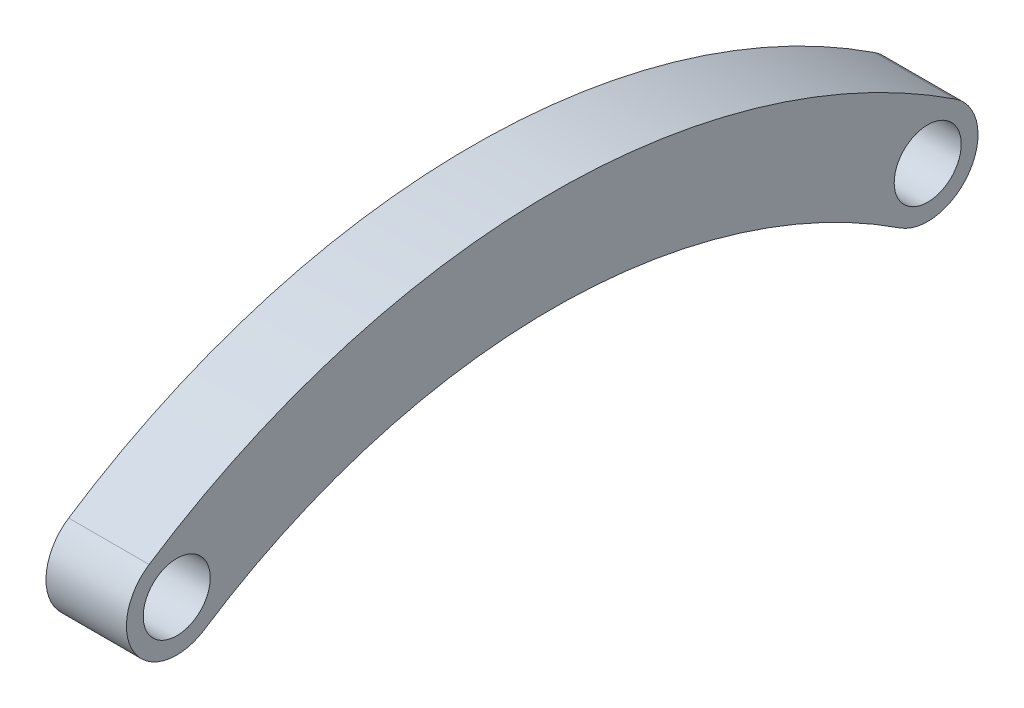
SolidWorks part; units mm, degrees
ref_plane "Front Plane" through (0, 0, 0) normal (0, 0, 1) x (1, 0, 0)
ref_plane "Top Plane" through (0, 0, 0) normal (0, 1, 0) x (1, 0, 0)
ref_plane "Right Plane" through (0, 0, 0) normal (1, 0, 0) x (0, 0, -1)
sketch "Sketch1" plane through (0, 0, 0) normal (1, 0, 0) x (0, 0, -1)
  line L0 (0, 55) -> (0, -55) construction
  line L1 (0, 0) -> (0, 6) construction
  line L2 (-22.4, -6.7) -> (22.4, -6.7) construction
  line L3 (81.1274, 6) -> (-72.2732, 6) construction
  line L4 (-25.4, 29.1562) -> (-25.4, -3.7) construction
  line L5 (25.4, 30.6853) -> (25.4, -3.7) construction
  arc A0 (0, 0) -> (20.7527, -6.2073) centre (0, -37.7948) cw
  arc A1 (0, 6) -> (24.0473, -1.1927) centre (0, -37.7948) cw
  arc A2 (20.7527, -6.2073) -> (24.0473, -1.1927) centre (22.4, -3.7) ccw
  arc A3 (-20.7527, -6.2073) -> (-24.0473, -1.1927) centre (-22.4, -3.7) cw
  arc A4 (0, 6) -> (-24.0473, -1.1927) centre (0, -37.7948) ccw
  arc A5 (0, 0) -> (-20.7527, -6.2073) centre (0, -37.7948) ccw
  circle A6 centre (22.4, -3.7) radius 2 construction
  dimension "D4" = 4
  dimension "D2" = 12.7
  dimension "D3" = 50.8
  dimension "D1" = 6
extrude "Boss-Extrude1" add sketch "Sketch1" along normal mid plane 4.8
sketch "Sketch2" plane through (2.4, 0, 0) normal (1, 0, 0) x (0, 0, -1)
  line L0 (0, 55) -> (0, -55) construction
  circle A0 centre (-22.4, -3.7) radius 2
  arc A1 (-24.0473, -1.1927) -> (-20.7527, -6.2073) centre (-22.4, -3.7) ccw construction
  circle A2 centre (22.4, -3.7) radius 2
  dimension "D1" = 4
extrude "Cut-Extrude1" cut sketch "Sketch2" against normal up to surface (4.8 mm away) up to face at (-2.4, -1.1736, 0)
